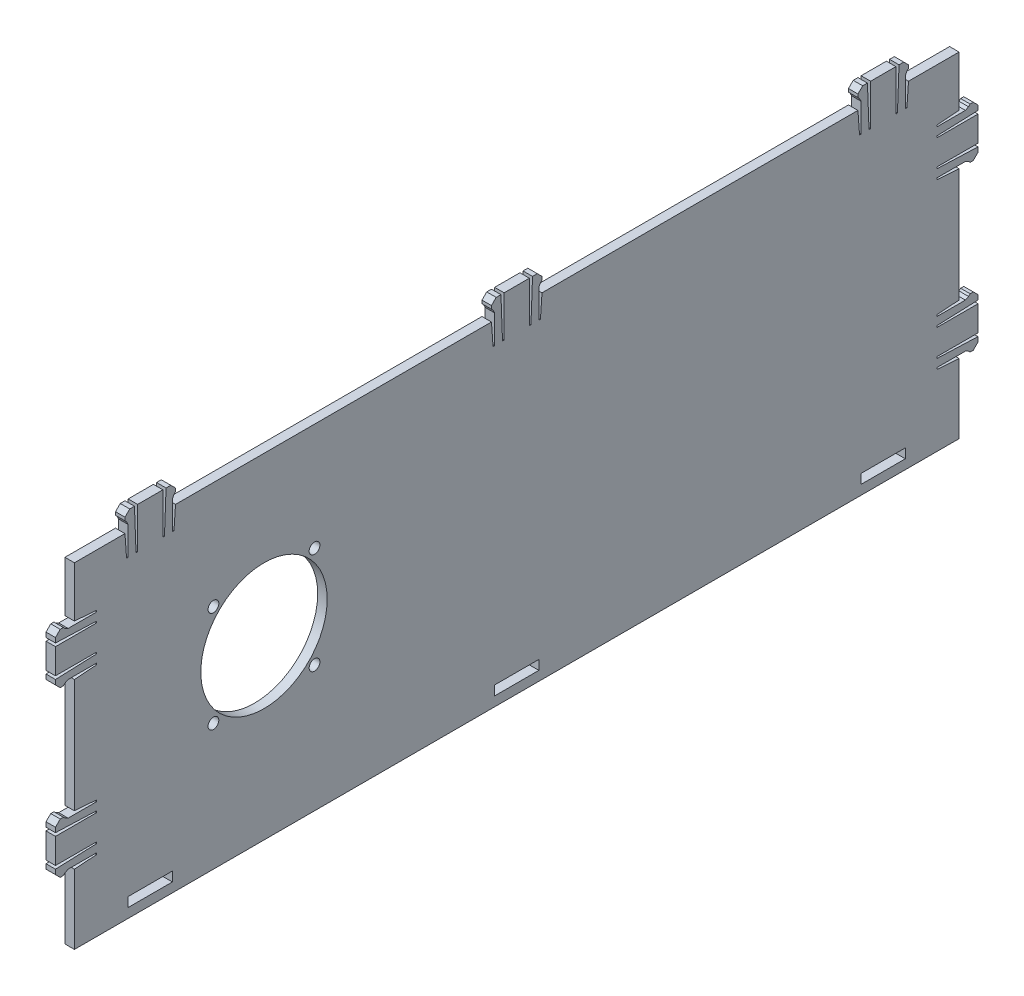
SolidWorks part; units mm, degrees
ref_plane "Front Plane" through (0, 0, 0) normal (0, 0, 1) x (1, 0, 0)
ref_plane "Top Plane" through (0, 0, 0) normal (0, 1, 0) x (1, 0, 0)
ref_plane "Right Plane" through (0, 0, 0) normal (1, 0, 0) x (0, 0, -1)
sketch "Sketch1" plane through (0, 0, 0) normal (1, 0, 0) x (0, 0, -1)
  line L0 (-140, 34) -> (-140, 50)
  line L1 (-124, 50) -> (-140, 50)
  line L2 (-140, -34) -> (-140, -56)
  line L3 (-140, -56) -> (140, -56)
  line L4 (140, 34) -> (140, 50)
  line L5 (-140, 18) -> (-140, -18)
  line L6 (-140, -34) -> (-132.9978, -33.5)
  line L7 (-132.9978, -33.5) -> (-132.9978, -33)
  line L8 (-132.9978, -33) -> (-141.9978, -33)
  line L9 (-141.9978, -33) -> (-142.9978, -33.5)
  line L10 (-142.9978, -33.5) -> (-143.4978, -34)
  line L11 (-143.4978, -34) -> (-144.4978, -34)
  line L12 (-144.4978, -34) -> (-145.9978, -32.5)
  line L13 (-145.9978, -32.5) -> (-145.9978, -31)
  line L14 (-145.9978, -31) -> (-132.9978, -30.5)
  line L15 (-132.9978, -30.5) -> (-132.9978, -30)
  line L16 (-132.9978, -30) -> (-145.9978, -30)
  line L17 (-132.9978, -22) -> (-145.9978, -22)
  line L18 (-132.9978, -21.5) -> (-132.9978, -22)
  line L19 (-145.9978, -21) -> (-132.9978, -21.5)
  line L20 (-145.9978, -19.5) -> (-145.9978, -21)
  line L21 (-144.4978, -18) -> (-145.9978, -19.5)
  line L22 (-143.4978, -18) -> (-144.4978, -18)
  line L23 (-142.9978, -18.5) -> (-143.4978, -18)
  line L24 (-141.9978, -19) -> (-142.9978, -18.5)
  line L25 (-132.9978, -19) -> (-141.9978, -19)
  line L26 (-132.9978, -18.5) -> (-132.9978, -19)
  line L27 (-140, -18) -> (-132.9978, -18.5)
  line L28 (-145.9978, -30) -> (-145.9978, -22)
  line L29 (-140, 18) -> (-132.9978, 18.5)
  line L30 (-132.9978, 18.5) -> (-132.9978, 19)
  line L31 (-132.9978, 19) -> (-141.9978, 19)
  line L32 (-141.9978, 19) -> (-142.9978, 18.5)
  line L33 (-142.9978, 18.5) -> (-143.4978, 18)
  line L34 (-143.4978, 18) -> (-144.4978, 18)
  line L35 (-144.4978, 18) -> (-145.9978, 19.5)
  line L36 (-145.9978, 19.5) -> (-145.9978, 21)
  line L37 (-145.9978, 21) -> (-132.9978, 21.5)
  line L38 (-132.9978, 21.5) -> (-132.9978, 22)
  line L39 (-132.9978, 22) -> (-145.9978, 22)
  line L40 (-132.9978, 30) -> (-145.9978, 30)
  line L41 (-132.9978, 30.5) -> (-132.9978, 30)
  line L42 (-145.9978, 31) -> (-132.9978, 30.5)
  line L43 (-145.9978, 32.5) -> (-145.9978, 31)
  line L44 (-144.4978, 34) -> (-145.9978, 32.5)
  line L45 (-143.4978, 34) -> (-144.4978, 34)
  line L46 (-142.9978, 33.5) -> (-143.4978, 34)
  line L47 (-141.9978, 33) -> (-142.9978, 33.5)
  line L48 (-132.9978, 33) -> (-141.9978, 33)
  line L49 (-132.9978, 33.5) -> (-132.9978, 33)
  line L50 (-140, 34) -> (-132.9978, 33.5)
  line L51 (-145.9978, 22) -> (-145.9978, 30)
  line L52 (140, -34) -> (140, -56)
  line L53 (140, -18) -> (140, 18)
  line L54 (140, 34) -> (132.9978, 33.5)
  line L55 (132.9978, 33.5) -> (132.9978, 33)
  line L56 (132.9978, 33) -> (141.9978, 33)
  line L57 (141.9978, 33) -> (142.9978, 33.5)
  line L58 (142.9978, 33.5) -> (143.4978, 34)
  line L59 (143.4978, 34) -> (144.4978, 34)
  line L60 (144.4978, 34) -> (145.9978, 32.5)
  line L61 (145.9978, 32.5) -> (145.9978, 31)
  line L62 (145.9978, 31) -> (132.9978, 30.5)
  line L63 (132.9978, 30.5) -> (132.9978, 30)
  line L64 (132.9978, 30) -> (145.9978, 30)
  line L65 (132.9978, 22) -> (145.9978, 22)
  line L66 (132.9978, 21.5) -> (132.9978, 22)
  line L67 (145.9978, 21) -> (132.9978, 21.5)
  line L68 (145.9978, 19.5) -> (145.9978, 21)
  line L69 (144.4978, 18) -> (145.9978, 19.5)
  line L70 (143.4978, 18) -> (144.4978, 18)
  line L71 (142.9978, 18.5) -> (143.4978, 18)
  line L72 (141.9978, 19) -> (142.9978, 18.5)
  line L73 (132.9978, 19) -> (141.9978, 19)
  line L74 (132.9978, 18.5) -> (132.9978, 19)
  line L75 (140, 18) -> (132.9978, 18.5)
  line L76 (145.9978, 30) -> (145.9978, 22)
  line L77 (140, -18) -> (132.9978, -18.5)
  line L78 (132.9978, -18.5) -> (132.9978, -19)
  line L79 (132.9978, -19) -> (141.9978, -19)
  line L80 (141.9978, -19) -> (142.9978, -18.5)
  line L81 (142.9978, -18.5) -> (143.4978, -18)
  line L82 (143.4978, -18) -> (144.4978, -18)
  line L83 (144.4978, -18) -> (145.9978, -19.5)
  line L84 (145.9978, -19.5) -> (145.9978, -21)
  line L85 (145.9978, -21) -> (132.9978, -21.5)
  line L86 (132.9978, -21.5) -> (132.9978, -22)
  line L87 (132.9978, -22) -> (145.9978, -22)
  line L88 (132.9978, -30) -> (145.9978, -30)
  line L89 (132.9978, -30.5) -> (132.9978, -30)
  line L90 (145.9978, -31) -> (132.9978, -30.5)
  line L91 (145.9978, -32.5) -> (145.9978, -31)
  line L92 (144.4978, -34) -> (145.9978, -32.5)
  line L93 (143.4978, -34) -> (144.4978, -34)
  line L94 (142.9978, -33.5) -> (143.4978, -34)
  line L95 (141.9978, -33) -> (142.9978, -33.5)
  line L96 (132.9978, -33) -> (141.9978, -33)
  line L97 (132.9978, -33.5) -> (132.9978, -33)
  line L98 (140, -34) -> (132.9978, -33.5)
  line L99 (145.9978, -22) -> (145.9978, -30)
  line L100 (124, 50) -> (140, 50)
  line L101 (-108, 50) -> (-8, 50)
  line L102 (8, 50) -> (108, 50)
  line L103 (-124, 50) -> (-123.5, 42.9978)
  line L104 (-123.5, 42.9978) -> (-123, 42.9978)
  line L105 (-123, 42.9978) -> (-123, 51.9978)
  line L106 (-123, 51.9978) -> (-123.5, 52.9978)
  line L107 (-123.5, 52.9978) -> (-124, 53.4978)
  line L108 (-124, 53.4978) -> (-124, 54.4978)
  line L109 (-124, 54.4978) -> (-122.5, 55.9978)
  line L110 (-122.5, 55.9978) -> (-121, 55.9978)
  line L111 (-121, 55.9978) -> (-120.5, 42.9978)
  line L112 (-120.5, 42.9978) -> (-120, 42.9978)
  line L113 (-120, 42.9978) -> (-120, 55.9978)
  line L114 (-116, 50) -> (-116, 55.7386) construction
  line L115 (-112, 42.9978) -> (-112, 55.9978)
  line L116 (-111.5, 42.9978) -> (-112, 42.9978)
  line L117 (-111, 55.9978) -> (-111.5, 42.9978)
  line L118 (-109.5, 55.9978) -> (-111, 55.9978)
  line L119 (-108, 54.4978) -> (-109.5, 55.9978)
  line L120 (-108, 53.4978) -> (-108, 54.4978)
  line L121 (-108.5, 52.9978) -> (-108, 53.4978)
  line L122 (-109, 51.9978) -> (-108.5, 52.9978)
  line L123 (-109, 42.9978) -> (-109, 51.9978)
  line L124 (-108.5, 42.9978) -> (-109, 42.9978)
  line L125 (-108, 50) -> (-108.5, 42.9978)
  line L126 (-120, 55.9978) -> (-112, 55.9978)
  line L127 (-8, 50) -> (-7.5, 42.9978)
  line L128 (-7.5, 42.9978) -> (-7, 42.9978)
  line L129 (-7, 42.9978) -> (-7, 51.9978)
  line L130 (-7, 51.9978) -> (-7.5, 52.9978)
  line L131 (-7.5, 52.9978) -> (-8, 53.4978)
  line L132 (-8, 53.4978) -> (-8, 54.4978)
  line L133 (-8, 54.4978) -> (-6.5, 55.9978)
  line L134 (-6.5, 55.9978) -> (-5, 55.9978)
  line L135 (-5, 55.9978) -> (-4.5, 42.9978)
  line L136 (-4.5, 42.9978) -> (-4, 42.9978)
  line L137 (-4, 42.9978) -> (-4, 55.9978)
  line L138 (0, 50) -> (0, 55.7386) construction
  line L139 (4, 42.9978) -> (4, 55.9978)
  line L140 (4.5, 42.9978) -> (4, 42.9978)
  line L141 (5, 55.9978) -> (4.5, 42.9978)
  line L142 (6.5, 55.9978) -> (5, 55.9978)
  line L143 (8, 54.4978) -> (6.5, 55.9978)
  line L144 (8, 53.4978) -> (8, 54.4978)
  line L145 (7.5, 52.9978) -> (8, 53.4978)
  line L146 (7, 51.9978) -> (7.5, 52.9978)
  line L147 (7, 42.9978) -> (7, 51.9978)
  line L148 (7.5, 42.9978) -> (7, 42.9978)
  line L149 (8, 50) -> (7.5, 42.9978)
  line L150 (-4, 55.9978) -> (4, 55.9978)
  line L151 (108, 50) -> (108.5, 42.9978)
  line L152 (108.5, 42.9978) -> (109, 42.9978)
  line L153 (109, 42.9978) -> (109, 51.9978)
  line L154 (109, 51.9978) -> (108.5, 52.9978)
  line L155 (108.5, 52.9978) -> (108, 53.4978)
  line L156 (108, 53.4978) -> (108, 54.4978)
  line L157 (108, 54.4978) -> (109.5, 55.9978)
  line L158 (109.5, 55.9978) -> (111, 55.9978)
  line L159 (111, 55.9978) -> (111.5, 42.9978)
  line L160 (111.5, 42.9978) -> (112, 42.9978)
  line L161 (112, 42.9978) -> (112, 55.9978)
  line L162 (116, 50) -> (116, 55.7386) construction
  line L163 (120, 42.9978) -> (120, 55.9978)
  line L164 (120.5, 42.9978) -> (120, 42.9978)
  line L165 (121, 55.9978) -> (120.5, 42.9978)
  line L166 (122.5, 55.9978) -> (121, 55.9978)
  line L167 (124, 54.4978) -> (122.5, 55.9978)
  line L168 (124, 53.4978) -> (124, 54.4978)
  line L169 (123.5, 52.9978) -> (124, 53.4978)
  line L170 (123, 51.9978) -> (123.5, 52.9978)
  line L171 (123, 42.9978) -> (123, 51.9978)
  line L172 (123.5, 42.9978) -> (123, 42.9978)
  line L173 (124, 50) -> (123.5, 42.9978)
  line L174 (112, 55.9978) -> (120, 55.9978)
  point P12 (-140, -34)
  point P37 (-140, 18)
  point P61 (140, 34)
  point P62 (140, 18)
  point P63 (140, 18)
  point P86 (140, -18)
  point P87 (140, -34)
  point P88 (140, -34)
  point P117 (-124, 50)
  point P143 (-8, 50)
  point P168 (108, 50)
  dimension "D1" = 280
  dimension "D2" = 106
  dimension "D3" = 140
  dimension "D4" = 50
  dimension "D5" = 16
  dimension "D6" = 36
  dimension "D7" = 7.0022
  dimension "D8" = 0.5
  dimension "D9" = 0.5
  dimension "D10" = 9
  dimension "D11" = 1
  dimension "D12" = 0.5
  dimension "D13" = 0.5
  dimension "D14" = 0.5
  dimension "D15" = 1
  dimension "D16" = 1.5
  dimension "D17" = 1.5
  dimension "D18" = 1.5
  dimension "D19" = 13
  dimension "D20" = 0.5
  dimension "D21" = 0.5
  dimension "D22" = 13
  dimension "D23" = 8
  dimension "D24" = 13
  dimension "D25" = 0.5
  dimension "D26" = 13
  dimension "D27" = 0.5
  dimension "D28" = 1.5
  dimension "D29" = 1.5
  dimension "D30" = 1.5
  dimension "D31" = 1
  dimension "D32" = 0.5
  dimension "D33" = 0.5
  dimension "D34" = 1
  dimension "D35" = 0.5
  dimension "D36" = 9
  dimension "D37" = 0.5
  dimension "D38" = 7.0022
  dimension "D39" = 0.5
  dimension "D40" = 7.0022
  dimension "D41" = 0.5
  dimension "D42" = 0.5
  dimension "D43" = 9
  dimension "D44" = 1
  dimension "D45" = 0.5
  dimension "D46" = 0.5
  dimension "D47" = 0.5
  dimension "D48" = 1
  dimension "D49" = 1.5
  dimension "D50" = 1.5
  dimension "D51" = 1.5
  dimension "D52" = 13
  dimension "D53" = 0.5
  dimension "D54" = 0.5
  dimension "D55" = 13
  dimension "D56" = 8
  dimension "D57" = 13
  dimension "D58" = 0.5
  dimension "D59" = 13
  dimension "D60" = 0.5
  dimension "D61" = 1.5
  dimension "D62" = 1.5
  dimension "D63" = 1.5
  dimension "D64" = 1
  dimension "D65" = 0.5
  dimension "D66" = 0.5
  dimension "D67" = 1
  dimension "D68" = 0.5
  dimension "D69" = 9
  dimension "D70" = 0.5
  dimension "D71" = 7.0022
  dimension "D72" = 0.5
  dimension "D73" = 16
  dimension "D74" = 36
  dimension "D75" = 7.0022
  dimension "D76" = 0.5
  dimension "D77" = 0.5
  dimension "D78" = 9
  dimension "D79" = 1
  dimension "D80" = 0.5
  dimension "D81" = 0.5
  dimension "D82" = 0.5
  dimension "D83" = 1
  dimension "D84" = 1.5
  dimension "D85" = 1.5
  dimension "D86" = 1.5
  dimension "D87" = 13
  dimension "D88" = 0.5
  dimension "D89" = 0.5
  dimension "D90" = 13
  dimension "D91" = 8
  dimension "D92" = 13
  dimension "D93" = 0.5
  dimension "D94" = 13
  dimension "D95" = 1.5
  dimension "D96" = 1.5
  dimension "D97" = 1.5
  dimension "D98" = 1
  dimension "D99" = 0.5
  dimension "D100" = 0.5
  dimension "D101" = 1
  dimension "D102" = 0.5
  dimension "D103" = 9
  dimension "D104" = 0.5
  dimension "D105" = 7.0022
  dimension "D106" = 0.5
  dimension "D107" = 7.0022
  dimension "D108" = 0.5
  dimension "D109" = 0.5
  dimension "D110" = 9
  dimension "D111" = 1
  dimension "D112" = 0.5
  dimension "D113" = 0.5
  dimension "D114" = 0.5
  dimension "D115" = 1
  dimension "D116" = 1.5
  dimension "D117" = 1.5
  dimension "D118" = 1.5
  dimension "D119" = 13
  dimension "D120" = 0.5
  dimension "D121" = 0.5
  dimension "D122" = 13
  dimension "D123" = 8
  dimension "D124" = 13
  dimension "D125" = 0.5
  dimension "D126" = 13
  dimension "D127" = 1.5
  dimension "D128" = 1.5
  dimension "D129" = 1.5
  dimension "D130" = 1
  dimension "D131" = 0.5
  dimension "D132" = 0.5
  dimension "D133" = 1
  dimension "D134" = 0.5
  dimension "D135" = 9
  dimension "D136" = 0.5
  dimension "D137" = 7.0022
  dimension "D138" = 0.5
  dimension "D139" = 22
  dimension "D140" = 0.5
  dimension "D141" = 16
  dimension "D142" = 100
  dimension "D143" = 100
  dimension "D144" = 0.5
  dimension "D145" = 9
  dimension "D146" = 0.5
  dimension "D147" = 1
  dimension "D148" = 0.5
  dimension "D149" = 0.5
  dimension "D150" = 1
  dimension "D151" = 1.5
  dimension "D152" = 1.5
  dimension "D153" = 0.5
  dimension "D154" = 0.5
  dimension "D155" = 13
  dimension "D156" = 7.0022
  dimension "D157" = 1.5
  dimension "D158" = 13
  dimension "D159" = 8
  dimension "D160" = 8
  dimension "D161" = 0.5
  dimension "D162" = 9
  dimension "D163" = 0.5
  dimension "D164" = 1
  dimension "D165" = 0.5
  dimension "D166" = 0.5
  dimension "D167" = 1
  dimension "D168" = 1.5
  dimension "D169" = 1.5
  dimension "D170" = 0.5
  dimension "D171" = 0.5
  dimension "D172" = 13
  dimension "D173" = 7.0022
  dimension "D174" = 1.5
  dimension "D175" = 13
  dimension "D176" = 8
  dimension "D177" = 8
  dimension "D178" = 0.5
  dimension "D179" = 9
  dimension "D180" = 0.5
  dimension "D181" = 1
  dimension "D182" = 0.5
  dimension "D183" = 0.5
  dimension "D184" = 1
  dimension "D185" = 1.5
  dimension "D186" = 1.5
  dimension "D187" = 0.5
  dimension "D188" = 0.5
  dimension "D189" = 13
  dimension "D190" = 7.0022
  dimension "D191" = 1.5
  dimension "D192" = 13
  dimension "D193" = 8
  dimension "D194" = 8
  dimension "D195" = 7.02
  dimension "D196" = 7.02
  dimension "D197" = 0.5
extrude "Boss-Extrude1" add sketch "Sketch1" along normal blind 3
sketch "Sketch3" plane through (3, 0, 0) normal (1, 0, 0) x (0, 0, -1)
  line L1 (-123, -50) -> (-109, -50)
  line L2 (-123, -50) -> (-123, -53)
  line L3 (-123, -53) -> (-109, -53)
  line L4 (-109, -50) -> (-109, -53)
  line L5 (-7, -50) -> (7, -50)
  line L6 (-7, -50) -> (-7, -53)
  line L7 (-7, -53) -> (7, -53)
  line L8 (7, -50) -> (7, -53)
  line L9 (123, -50) -> (109, -50)
  line L10 (123, -50) -> (123, -53)
  line L11 (123, -53) -> (109, -53)
  line L12 (109, -50) -> (109, -53)
  dimension "D1" = 14
  dimension "D2" = 3
  dimension "D3" = 109
  dimension "D4" = 50
  dimension "D5" = 14
  dimension "D6" = 3
  dimension "D7" = 50
  dimension "D8" = 7
  dimension "D9" = 14
  dimension "D10" = 3
  dimension "D11" = 50
  dimension "D12" = 109
extrude "Cut-Extrude1" cut sketch "Sketch3" against normal blind 3
sketch "Sketch6" plane through (3, 0, 0) normal (1, 0, 0) x (0, 0, -1)
  text T0 "BOXZ2" font "Century Gothic" height in points 22
  dimension "D1" = 11.2
  dimension "D2" = 0
sketch "Sketch7" plane through (3, 0, 0) normal (1, 0, 0) x (0, 0, -1)
  circle A0 centre (-80, 0) radius 20
  dimension "D1" = 40
  dimension "D2" = 80
  dimension "D3" = 50
extrude "Cut-Extrude2" cut sketch "Sketch7" against normal blind 3
sketch "Sketch9" plane through (3, 0, 0) normal (1, 0, 0) x (0, 0, -1)
  circle A0 centre (-96, 16) radius 1.7
  circle A1 centre (-64, 16) radius 1.7
  circle A2 centre (-64, -16) radius 1.7
  circle A3 centre (-96, -16) radius 1.7
  point P0 (-80, 0)
  dimension "D1" = 3.4
  dimension "D2" = 3.4
  dimension "D3" = 3.4
  dimension "D4" = 3.4
  dimension "D5" = 16
  dimension "D6" = 16
  dimension "D7" = 16
  dimension "D8" = 16
  dimension "D9" = 16
  dimension "D10" = 16
  dimension "D11" = 16
  dimension "D12" = 16
extrude "Cut-Extrude3" cut sketch "Sketch9" against normal blind 3
